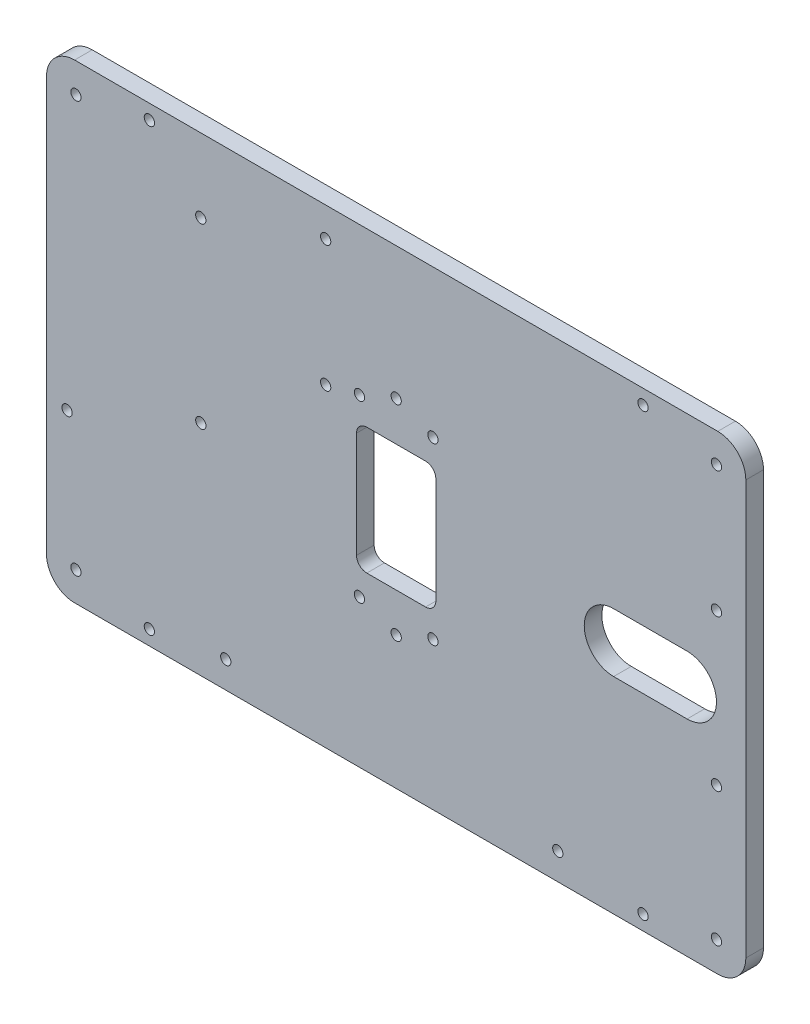
SolidWorks part; units mm, degrees
ref_plane "Plan de face" through (0, 0, 0) normal (0, 0, 1) x (1, 0, 0)
ref_plane "Plan de dessus" through (0, 0, 0) normal (0, 1, 0) x (1, 0, 0)
ref_plane "Plan de droite" through (0, 0, 0) normal (1, 0, 0) x (0, 0, -1)
sketch "Esquisse1" plane through (0, 0, 0) normal (0, 0, 1) x (1, 0, 0)
  line L1 (109, -70) -> (-109, -70) construction
  line L2 (109, -70) -> (109, 70) construction
  line L3 (109, 70) -> (-109, 70) construction
  line L4 (-109, -70) -> (-109, 70) construction
  line L5 (-13.5, 21.5) -> (13.5, 21.5)
  line L11 (109, -70) -> (109, -27) construction
  line L12 (109, 48.5) -> (58.5, 48.5) construction
  line L13 (-112, -24.5) -> (109, -24.5) construction
  line L14 (109.4508, 80) -> (-109.4508, 80)
  line L15 (-119, -70.4508) -> (-119, 70.4508)
  line L16 (109.4508, -80) -> (-109.4508, -80)
  line L17 (119, -70.4508) -> (119, 70.4508)
  line L18 (-119, -80) -> (-119, 80) construction
  line L19 (119, -80) -> (-119, -80) construction
  line L20 (119, -80) -> (119, 80) construction
  line L21 (119, 80) -> (-119, 80) construction
  line L22 (84, 75) -> (84, -75) construction
  line L29 (0, 0) -> (0, -24.5) construction
  line L36 (109, 27) -> (-24, 27) construction
  line L37 (109, 27) -> (109, 70) construction
  line L38 (109, 70) -> (-24, 70) construction
  line L39 (-24, 27) -> (-24, 70) construction
  line L40 (109, 27) -> (-24, 70) construction
  line L41 (109, 70) -> (-24, 27) construction
  line L45 (99, 0) -> (74, 0) construction
  line L47 (99, -10) -> (74, -10)
  line L48 (0, -16.25) -> (0, -34.75) construction
  line L49 (0, 16.5) -> (0, 35) construction
  line L50 (0, 16.5) -> (-24, 16.5) construction
  line L53 (0, 16.5) -> (0, 0) construction
  line L55 (-24, 27) -> (-24, -27) construction
  line L56 (-12, 0) -> (-24, 0) construction
  line L57 (97, 0) -> (109, 0) construction
  line L59 (0, -16.25) -> (0, 0) construction
  line L61 (0, -16.25) -> (-24, -16.25) construction
  line L62 (99, 10) -> (74, 10)
  line L68 (13.5, -21.5) -> (13.5, 21.5)
  line L69 (-13.5, -21.5) -> (-13.5, 21.5)
  line L70 (13.5, -21.5) -> (-13.5, -21.5)
  line L76 (-127, 55) -> (-66.5, 55) construction
  line L77 (-127, 55) -> (-127, -5.5) construction
  line L82 (-127, -5.5) -> (-66.5, -5.5) construction
  line L83 (-66.5, 55) -> (-66.5, -5.5) construction
  circle A2 centre (109, -70) radius 1.75
  circle A3 centre (109, 70) radius 1.75
  arc A10 (-119, -70.4508) -> (-109.4508, -80) centre (-109.4508, -70.4508) ccw
  arc A11 (119, -70.4508) -> (109.4508, -80) centre (109.4508, -70.4508) cw
  arc A12 (109.4508, 80) -> (119, 70.4508) centre (109.4508, 70.4508) cw
  arc A13 (-109.4508, 80) -> (-119, 70.4508) centre (-109.4508, 70.4508) ccw
  circle A15 centre (-24, 27) radius 1.75
  circle A16 centre (-24, 70) radius 1.75
  circle A17 centre (109, 27) radius 1.75
  circle A34 centre (109, -24.5) radius 1.75
  circle A35 centre (-112, -24.5) radius 1.75
  circle A36 centre (84, 75) radius 1.75
  circle A37 centre (84, -75) radius 1.75
  circle A40 centre (-109, -70) radius 1.75
  circle A41 centre (-109, 70) radius 1.75
  circle A42 centre (-84, -75) radius 1.75
  circle A43 centre (-84, 75) radius 1.75
  circle A51 centre (0, 35) radius 1.75
  circle A52 centre (0, -34.75) radius 1.75
  circle A53 centre (-12.5, 29.75) radius 1.75
  circle A54 centre (12.5, 29.75) radius 1.75
  circle A55 centre (12.5, -29.75) radius 1.75
  circle A56 centre (-12.5, -29.75) radius 1.75
  arc A57 (99, -10) -> (99, 10) centre (99, 0) ccw
  arc A58 (74, 10) -> (74, -10) centre (74, 0) ccw
  circle A70 centre (-66.5, 55) radius 1.75
  circle A71 centre (-66.5, -5.5) radius 1.75
  circle A74 centre (-58, -70.9) radius 1.75
  circle A75 centre (55, -70.9) radius 1.75
  circle A76 centre (55, -70.9) radius 1.75 construction
  circle A77 centre (-58, -70.9) radius 1.75 construction
  point P14 (84, 0)
  point P48 (42.5, 48.5)
  point P49 (0, 0)
  point P70 (86.5, 0)
  point P72 (-13.5, 0)
  point P74 (0, 0)
  point P84 (64, 0)
  point P107 (-119, 0)
  dimension "D3" = 3.5
  dimension "D6" = 221
  dimension "D9" = 9.5492
  dimension "D10" = 5
  dimension "D18" = 18.5
  dimension "D4" = 45.5
  dimension "D12" = 50.5
  dimension "D13" = 27
  dimension "D19" = 45
  dimension "D5" = 13.5
  dimension "D11" = 16.5
  dimension "D21" = 60.5
  dimension "D1" = 140
  dimension "D2" = 218
  dimension "D7" = 25
  dimension "D14" = 12
  dimension "D15" = 20
  dimension "D16" = 43
  dimension "D17" = 133
  dimension "D20" = 16.25
  dimension "D22" = 42.5
  dimension "D23" = 15
  dimension "D8" = 10
extrude "Boss.-Extru.1" add sketch "Esquisse1" along normal blind 6
fillet "Congé1" radius 3.5 4 edges at (13.5, 21.5, 3) (-13.5, 21.5, 3) (13.5, -21.5, 3) (-13.5, -21.5, 3)
